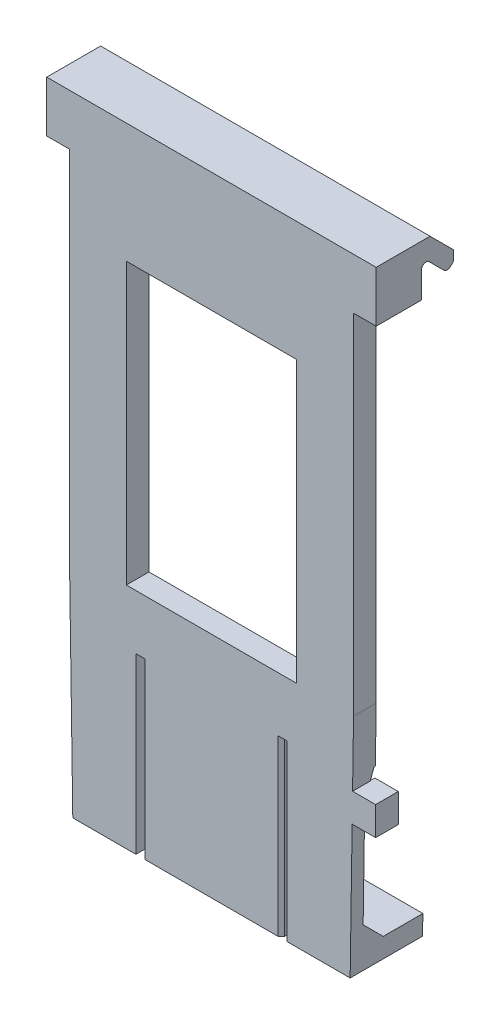
SolidWorks part; units mm, degrees
ref_plane "Front Plane" through (0, 0, 0) normal (0, 0, 1) x (1, 0, 0)
ref_plane "Top Plane" through (0, 0, 0) normal (0, 1, 0) x (1, 0, 0)
ref_plane "Right Plane" through (0, 0, 0) normal (1, 0, 0) x (0, 0, -1)
sketch "Sketch1" plane through (0, 0, 0) normal (0, 0, 1) x (1, 0, 0)
  line L0 (20.0634, 43.434) -> (5.0266, 43.434) construction
  line L1 (20.0634, 18.669) -> (20.0634, 43.434) construction
  line L2 (5.0266, 18.669) -> (20.0634, 18.669) construction
  line L3 (5.0266, 43.434) -> (5.0266, 18.669) construction
  line L4 (20.0634, 43.434) -> (5.0266, 43.434)
  line L5 (20.0634, 18.669) -> (20.0634, 43.434)
  line L6 (5.0266, 18.669) -> (20.0634, 18.669)
  line L7 (5.0266, 43.434) -> (5.0266, 18.669)
  line L8 (21.3334, 45.085) -> (3.7566, 45.085) construction
  line L9 (3.7566, 45.085) -> (3.7566, 13.843) construction
  line L10 (21.3334, 13.843) -> (21.3334, 45.085) construction
  line L11 (3.7566, 13.843) -> (21.3334, 13.843) construction
  line L12 (21.3334, 45.085) -> (3.7566, 45.085)
  line L13 (3.7566, 45.085) -> (3.7566, 13.843)
  line L14 (21.3334, 13.843) -> (21.3334, 45.085)
  line L15 (3.7566, 13.843) -> (21.3334, 13.843)
  line L17 (3.7566, 13.843) -> (21.3334, 13.843)
  line L18 (3.7566, 13.843) -> (3.7566, 45.085)
  line L19 (3.7566, 45.085) -> (21.3334, 45.085)
  line L20 (21.3334, 13.843) -> (21.3334, 45.085)
  line L21 (5.0266, 18.669) -> (20.0634, 18.669)
  line L22 (5.0266, 18.669) -> (5.0266, 43.434)
  line L23 (5.0266, 43.434) -> (20.0634, 43.434)
  line L24 (20.0634, 18.669) -> (20.0634, 43.434)
extrude "Boss-Extrude1" add sketch "Sketch1" along normal blind 2 from offset 2 contours L13 L15 L14 L12 L7 L4 L5 L6
sketch "Sketch2" plane through (25.09, 0, 0) normal (1, 0, 0) x (0, 0, -1)
  line L0 (0, 51.49) -> (1.27, 51.49) construction
  line L1 (1.27, 2) -> (1.27, 51.49) construction
  line L2 (0, 2) -> (0, 51.49) construction
  line L3 (0, 51.49) -> (1.27, 51.49) construction
  line L4 (1.27, 2) -> (1.27, 51.49) construction
  line L5 (0, 2) -> (0, 51.49) construction
  line L6 (0, 51.49) -> (0, 49.49)
  line L8 (0, 51.49) -> (0, 51.7943)
  line L9 (0.6828, 52.0772) -> (1.27, 51.49)
  line L10 (1.27, 51.49) -> (1.9872, 50.7728)
  line L11 (2.5528, 50.7728) -> (2.8051, 51.0251)
  line L12 (2.8051, 51.9472) -> (0.758, 53.9943)
  line L14 (-4, 53.9943) -> (-4, 49.49)
  line L17 (-4, 53.9943) -> (0.758, 53.9943)
  line L18 (2.8051, 51.0251) -> (2.8051, 51.9472)
  line L19 (0, 49.49) -> (-4, 49.49)
  arc A0 (0.6828, 52.0772) -> (0, 51.7943) centre (0.4, 51.7943) ccw
  arc A1 (2.5528, 50.7728) -> (1.9872, 50.7728) centre (2.27, 51.0557) cw
  point P22 (2.27, 50.49)
  dimension "D4" = 0.4
  dimension "D5" = 0.4
  dimension "D6" = 2.2
  dimension "D1" = 45
  dimension "D2" = 1
  dimension "D3" = 90
  dimension "D8" = 4
extrude "Boss-Extrude2" add sketch "Sketch2" against normal offset from surface (29.09 mm away) 2 from offset 2 separate body
sketch "Sketch4" plane through (0, 0, 0) normal (0, -1, 0) x (1, 0, 0)
  line L0 (8.075, 1.96) -> (8.075, 1.25) construction
  line L5 (8.075, 1.96) -> (8.075, 1.25) construction
  line L6 (5.461, 1.905) -> (5.461, 0) construction
  line L7 (19.629, 1.905) -> (19.629, 0) construction
  line L8 (2, 0) -> (23.09, 0) construction
  line L9 (17.015, 1.25) -> (17.015, 1.96) construction
  line L10 (5.461, 1.905) -> (5.461, 0) construction
  line L11 (19.629, 1.905) -> (19.629, 0) construction
  line L12 (2, 0) -> (23.09, 0) construction
  line L13 (17.015, 1.25) -> (17.015, 1.96) construction
  line L14 (9.325, 3.21) -> (15.765, 3.21) construction
  line L15 (9.325, 0) -> (15.765, 0) construction
  line L16 (17.215, 1.25) -> (17.215, 1.96)
  line L17 (9.325, 3.41) -> (15.765, 3.41)
  line L18 (7.875, 1.96) -> (7.875, 1.25) construction
  line L19 (2, -0.2) -> (23.09, -0.2) construction
  line L20 (6.375, 1.96) -> (6.375, 1.25) construction
  line L21 (3.7566, 4) -> (21.3334, 4) construction
  line L22 (3.7566, 4) -> (21.3334, 4) construction
  line L23 (2, -1.7) -> (23.09, -1.7) construction
  line L24 (5.461, 1.905) -> (5.461, 4.5562) construction
  line L25 (19.629, 0) -> (19.629, -4.0911) construction
  line L26 (9.325, -0.2) -> (15.765, -0.2)
  line L27 (6.375, 4) -> (18.715, 4)
  line L28 (6.375, 4) -> (6.375, -1.7)
  line L29 (6.375, -1.7) -> (18.715, -1.7)
  line L30 (18.715, 4) -> (18.715, -1.7)
  line L31 (7.875, 1.96) -> (7.875, 1.25)
  arc A0 (9.325, 3.21) -> (8.075, 1.96) centre (9.325, 1.96) ccw construction
  arc A1 (8.075, 1.25) -> (9.325, 0) centre (9.325, 1.25) ccw construction
  arc A4 (8.075, 1.25) -> (9.325, 0) centre (9.325, 1.25) ccw construction
  arc A5 (9.325, 3.21) -> (8.075, 1.96) centre (9.325, 1.96) ccw construction
  arc A6 (15.765, 0) -> (17.015, 1.25) centre (15.765, 1.25) ccw construction
  arc A7 (17.015, 1.96) -> (15.765, 3.21) centre (15.765, 1.96) ccw construction
  arc A8 (15.765, 0) -> (17.015, 1.25) centre (15.765, 1.25) ccw construction
  arc A9 (17.015, 1.96) -> (15.765, 3.21) centre (15.765, 1.96) ccw construction
  arc A10 (15.765, -0.2) -> (17.215, 1.25) centre (15.765, 1.25) ccw
  arc A11 (17.215, 1.96) -> (15.765, 3.41) centre (15.765, 1.96) ccw
  arc A12 (9.325, 3.41) -> (7.875, 1.96) centre (9.325, 1.96) ccw
  arc A13 (7.875, 1.25) -> (9.325, -0.2) centre (9.325, 1.25) ccw
  dimension "D4" = 1.5
  dimension "D1" = 0.2
  dimension "D2" = 1.5
  dimension "D3" = 1.5
extrude "Boss-Extrude3" add sketch "Sketch4" along normal blind 1.5 separate body
sketch "Sketch5" plane through (0, 0, 0) normal (0, 1, 0) x (1, 0, 0)
  line L0 (7.8756, -2) -> (6.375, -2)
  line L1 (15.765, -3.41) -> (9.325, -3.41) construction
  line L2 (18.715, -2) -> (6.375, -2)
  line L3 (18.715, -2) -> (17.2144, -2)
  line L4 (18.715, 1.7) -> (18.715, -4) construction
  line L5 (18.715, -4) -> (6.375, -4) construction
  line L6 (6.375, -4) -> (6.375, 1.7) construction
  line L7 (15.765, -3.41) -> (9.325, -3.41)
  line L8 (18.715, -2) -> (18.715, -4)
  line L9 (18.715, -4) -> (6.375, -4)
  line L10 (6.375, -4) -> (6.375, -2)
  arc A0 (7.875, -1.96) -> (9.325, -3.41) centre (9.325, -1.96) ccw construction
  arc A1 (15.765, -3.41) -> (17.215, -1.96) centre (15.765, -1.96) ccw construction
  arc A2 (7.8756, -2) -> (9.325, -3.41) centre (9.325, -1.96) ccw
  arc A3 (15.765, -3.41) -> (17.2146, -1.9949) centre (15.765, -1.96) ccw
  line M2 (6.375, 1.7) -> (6.375, -4)
  line M3 (6.375, -4) -> (18.715, -4)
  line M4 (18.715, -4) -> (18.715, 1.7)
  arc M8 (17.215, -1.96) -> (15.765, -3.41) centre (15.765, -1.96) cw
  line M9 (15.765, -3.41) -> (9.325, -3.41)
  arc M10 (9.325, -3.41) -> (7.875, -1.96) centre (9.325, -1.96) cw
  dimension "D1" = 2
extrude "Boss-Extrude4" add sketch "Sketch5" along normal up to surface (13.843 mm away) contours L3 L0 M4 M8 M9 M10 M2 M3 up to face at (12.545, 13.843, 3)
sketch "Sketch6" plane through (0, 0, 2.905) normal (0, 0, 1) x (1, 0, 0)
  line L0 (6.375, 13.843) -> (6.375, 0) construction
  line L1 (6.375, 13.843) -> (6.375, 0) construction
  line L2 (2.7764, 3.3369) -> (2.7937, 4.0799) construction
  line L3 (4.9533, 4.0799) -> (4.9706, 3.3369) construction
  line L4 (2.7764, 3.3369) -> (2.7937, 4.0799) construction
  line L5 (4.9533, 4.0799) -> (4.9706, 3.3369) construction
  line L6 (3.7566, 13.843) -> (6.375, 13.843) construction
  line L7 (3.7566, 13.843) -> (6.375, 13.843) construction
  line L8 (18.715, -1.5) -> (6.375, -1.5) construction
  line L9 (18.715, -1.5) -> (6.375, -1.5) construction
  line L10 (6.125, 13.843) -> (6.125, -1.5)
  line L11 (6.125, -1.5) -> (0, -1.5)
  line L12 (0, -1.5) -> (0, 13.843)
  line L13 (0, 13.843) -> (6.125, 13.843)
  line L14 (0, 51.49) -> (0, 2) construction
  line L15 (0, 51.49) -> (0, 2) construction
  arc A0 (4.9533, 4.0799) -> (2.7937, 4.0799) centre (3.8735, 4.0547) ccw construction
  arc A1 (2.7764, 3.3369) -> (4.9706, 3.3369) centre (3.8735, 3.3113) ccw construction
  arc A2 (4.9533, 4.0799) -> (2.7937, 4.0799) centre (3.8735, 4.0547) ccw construction
  arc A3 (2.7764, 3.3369) -> (4.9706, 3.3369) centre (3.8735, 3.3113) ccw construction
  dimension "D1" = 0.5
extrude "Boss-Extrude5" add sketch "Sketch6" along normal up to surface (1.095 mm away) up to face at (12.545, 31.0515, 4)
sketch "Sketch9" plane through (0, 0, 2.905) normal (0, 0, 1) x (1, 0, 0)
  line L0 (25.09, 2) -> (25.09, 51.49) construction
  line L1 (18.715, 13.843) -> (18.715, -1.5) construction
  line L2 (20.1367, 4.0799) -> (20.1194, 3.3369)
  line L3 (22.3136, 3.3369) -> (22.2963, 4.0799)
  line L4 (20.1367, 4.0799) -> (20.1194, 3.3369) construction
  line L5 (22.3136, 3.3369) -> (22.2963, 4.0799) construction
  line L6 (18.715, 13.843) -> (21.3334, 13.843) construction
  line L7 (25.09, 2) -> (25.09, 51.49) construction
  line L8 (18.715, 13.843) -> (18.715, -1.5) construction
  line L9 (18.715, 13.843) -> (21.3334, 13.843) construction
  line L11 (18.965, 13.843) -> (25.09, 13.843)
  line L12 (18.965, 13.843) -> (18.965, -1.5)
  line L13 (18.965, -1.5) -> (25.09, -1.5)
  line L14 (25.09, 13.843) -> (25.09, -1.5)
  arc A2 (20.1194, 3.3369) -> (22.3136, 3.3369) centre (21.2165, 3.3113) ccw
  arc A3 (22.2963, 4.0799) -> (20.1367, 4.0799) centre (21.2165, 4.0547) ccw
  arc A4 (20.1194, 3.3369) -> (22.3136, 3.3369) centre (21.2165, 3.3113) ccw construction
  arc A5 (22.2963, 4.0799) -> (20.1367, 4.0799) centre (21.2165, 4.0547) ccw construction
  dimension "D2" = 0.5
  dimension "D1" = 0
extrude "Boss-Extrude6" add sketch "Sketch9" along normal up to surface (1.095 mm away) up to face at (12.545, 31.0515, 4)
sketch "Sketch10" plane through (0, 0, 4) normal (0, 0, 1) x (1, 0, 0)
  line L0 (-2, 49.49) -> (27.09, 49.49) construction
  line L1 (3.7566, 13.843) -> (0, 13.843) construction
  line L2 (3.7566, 45.085) -> (3.7566, 13.843) construction
  line L3 (21.3334, 45.085) -> (3.7566, 45.085) construction
  line L4 (21.3334, 13.843) -> (21.3334, 45.085) construction
  line L5 (25.09, 13.843) -> (21.3334, 13.843) construction
  line L6 (-2, 49.49) -> (27.09, 49.49) construction
  line L7 (3.7566, 13.843) -> (0, 13.843) construction
  line L8 (3.7566, 45.085) -> (3.7566, 13.843) construction
  line L9 (21.3334, 45.085) -> (3.7566, 45.085) construction
  line L10 (21.3334, 13.843) -> (21.3334, 45.085) construction
  line L11 (25.09, 13.843) -> (21.3334, 13.843) construction
  line L12 (25.09, 13.843) -> (25.09, 49.49) construction
  line L13 (0, 13.843) -> (0, 49.49) construction
  line L14 (25.09, 49.49) -> (25.09, 13.843)
  line L15 (25.09, 13.843) -> (21.3334, 13.843)
  line L16 (21.3334, 13.843) -> (21.3334, 45.085)
  line L17 (21.3334, 45.085) -> (3.7566, 45.085)
  line L18 (3.7566, 45.085) -> (3.7566, 13.843)
  line L19 (3.7566, 13.843) -> (0, 13.843)
  line L20 (0, 13.843) -> (0, 49.49)
  line L21 (0, 49.49) -> (25.09, 49.49)
extrude "Boss-Extrude7" add sketch "Sketch10" against normal up to surface (2 mm away) up to face at (12.545, 31.0515, 2)
chamfer "Chamfer1" distance 2.3 distance2 0.8 2 edges at (22.0275, 13.843, 2.905) (3.0625, 13.843, 2.905)
sketch "Sketch11" plane through (0, 0, 2.905) normal (0, 0, -1) x (-1, 0, 0)
  line L0 (0, 11.543) -> (0, -1.5) construction
  line L1 (-6.125, -1.5) -> (0, -1.5)
  line L2 (-6.125, -1.5) -> (-6.125, 0.25)
  line L3 (-6.125, 0.25) -> (0, 0.25)
  line L4 (0, -1.5) -> (0, 0.25)
  line L5 (-25.09, -1.5) -> (-25.09, 11.543) construction
  line L6 (-18.965, -1.5) -> (-25.09, -1.5)
  line L7 (-18.965, -1.5) -> (-18.965, 0.25)
  line L8 (-18.965, 0.25) -> (-25.09, 0.25)
  line L9 (-25.09, -1.5) -> (-25.09, 0.25)
  dimension "D1" = 1.75
  dimension "D2" = 1.75
extrude "Boss-Extrude9" add sketch "Sketch11" along normal blind 5.3
chamfer "Chamfer2" distance 1.8 angle 45 2 edges at (22.0275, 0.25, 2.905) (3.0625, 0.25, 2.905)
sketch "Sketch12" plane through (6.125, 0, 0) normal (1, 0, 0) x (0, 0, -1)
  line L8 (-4, 13.843) -> (-4, -1.5)
  line L9 (-4, -1.5) -> (2.395, -1.5)
  line L10 (2.395, -1.5) -> (2.395, 0.25)
  line L11 (2.395, 0.25) -> (-1.105, 0.25)
  line L12 (-1.105, 0.25) -> (-2.905, 2.05)
  line L13 (-2.905, 2.05) -> (-2.905, 11.543)
  line L14 (-2.905, 11.543) -> (-2.105, 13.843)
  line L15 (-2.105, 13.843) -> (-4, 13.843)
  line L16 (-4, 13.843) -> (-4, -1.5)
  line L17 (-4, -1.5) -> (2.395, -1.5)
  line L18 (2.395, -1.5) -> (2.395, 0.25)
  line L19 (2.395, 0.25) -> (-1.105, 0.25)
  line L20 (-1.105, 0.25) -> (-2.905, 2.05)
  line L21 (-2.905, 2.05) -> (-2.905, 11.543)
  line L22 (-2.905, 11.543) -> (-2.105, 13.843)
  line L23 (-2.105, 13.843) -> (-4, 13.843)
  dimension "D1" = 0
extrude "Cut-Extrude1" cut sketch "Sketch12" against normal blind 0.25
sketch "Sketch13" plane through (18.965, 0, 0) normal (-1, 0, 0) x (0, 0, 1)
  line L8 (4, -1.5) -> (4, 13.843)
  line L9 (4, 13.843) -> (2.105, 13.843)
  line L10 (2.105, 13.843) -> (2.905, 11.543)
  line L11 (2.905, 11.543) -> (2.905, 2.05)
  line L12 (2.905, 2.05) -> (1.105, 0.25)
  line L13 (1.105, 0.25) -> (-2.395, 0.25)
  line L14 (-2.395, 0.25) -> (-2.395, -1.5)
  line L15 (-2.395, -1.5) -> (4, -1.5)
  line L16 (4, -1.5) -> (4, 13.843)
  line L17 (4, 13.843) -> (2.105, 13.843)
  line L18 (2.105, 13.843) -> (2.905, 11.543)
  line L19 (2.905, 11.543) -> (2.905, 2.05)
  line L20 (2.905, 2.05) -> (1.105, 0.25)
  line L21 (1.105, 0.25) -> (-2.395, 0.25)
  line L22 (-2.395, 0.25) -> (-2.395, -1.5)
  line L23 (-2.395, -1.5) -> (4, -1.5)
  dimension "D1" = 0
extrude "Cut-Extrude2" cut sketch "Sketch13" against normal blind 0.25
sketch "Sketch14" plane through (0, 0, 4) normal (0, 0, 1) x (1, 0, 0)
  line L0 (25.09, 18.669) -> (24.79, -1.5)
  line L1 (25.09, -1.5) -> (25.09, 49.49) construction
  line L2 (19.215, -1.5) -> (25.09, -1.5) construction
  line L3 (24.79, -1.5) -> (25.09, -1.5)
  line L4 (25.09, -1.5) -> (25.09, 18.669)
  line L5 (0, 18.6698) -> (0.3, -1.5)
  line L6 (0, 49.49) -> (0, -1.5) construction
  line L7 (0, -1.5) -> (5.875, -1.5) construction
  line L8 (0.3, -1.5) -> (0, -1.5)
  line L9 (0, -1.5) -> (0, 18.6698)
  point P14 (0, 0)
  dimension "D1" = 0.3
  dimension "D2" = 0.3
extrude "Cut-Extrude3" cut sketch "Sketch14" against normal up to surface (6.395 mm away) up to face at (2.9375, -0.625, -2.395)
sketch "Sketch15" plane through (0, 0, 4) normal (0, 0, 1) x (1, 0, 0)
  line L0 (25.09, 18.669) -> (24.79, -1.5) construction
  line L1 (24.9663, 10.3545) -> (27.04, 10.3545)
  line L2 (24.9663, 10.3545) -> (24.9663, 12.8865)
  line L3 (24.9663, 12.8865) -> (27.04, 12.8865)
  line L4 (27.04, 10.3545) -> (27.04, 12.8865)
  line L5 (25.09, 10.1045) -> (27.09, 10.1045) construction
  line L6 (25.09, 13.1365) -> (27.09, 13.1365) construction
  line L7 (27.09, -1.5) -> (27.09, 10.1045) construction
  dimension "D1" = 0.25
  dimension "D2" = 0.25
  dimension "D3" = 0.05
extrude "Boss-Extrude10" add sketch "Sketch15" against normal blind 2
chamfer "Chamfer3" distance 0.3 angle 45 2 edges at (6.375, 6.1715, 4) (18.715, 6.1715, 4)
chamfer "Chamfer4" distance 2 angle 45 2 edges at (7.1253, 0, 2) (17.9647, 0, 2)
